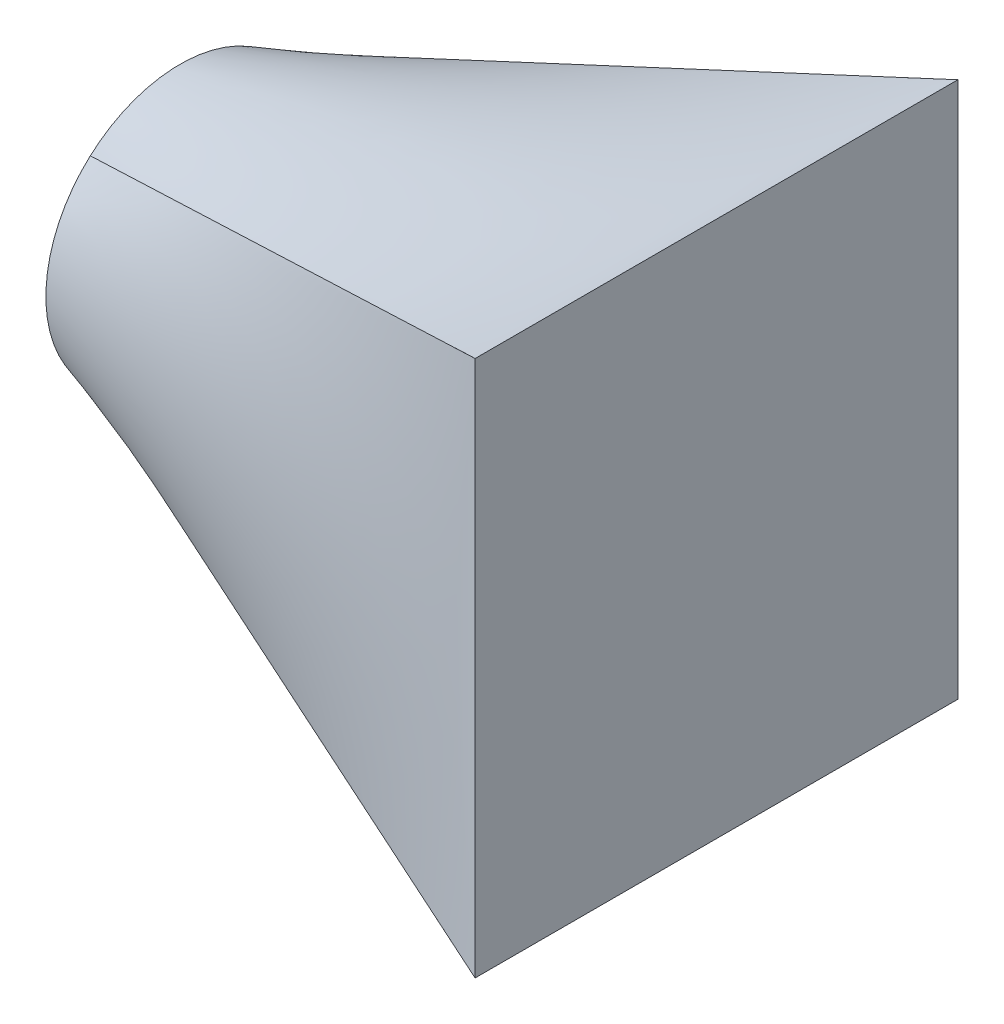
SolidWorks part; units mm, degrees
ref_plane "Přední rovina" through (0, 0, 0) normal (0, 0, 1) x (1, 0, 0)
ref_plane "Vrchní rovina" through (0, 0, 0) normal (0, 1, 0) x (1, 0, 0)
ref_plane "Pravá rovina" through (0, 0, 0) normal (1, 0, 0) x (0, 0, -1)
sketch "Skica1" plane through (0, 0, 0) normal (1, 0, 0) x (0, 0, -1)
  circle A0 centre (0, 0) radius 25
  dimension "D1" = 50
ref_plane "Rovina1" through (100, 0, 0) normal (1, 0, 0) x (0, 0, -1)
sketch "Skica2" plane through (100, 0, 0) normal (1, 0, 0) x (0, 0, -1)
  line L1 (-45, 50) -> (45, 50)
  line L2 (-45, 50) -> (-45, -50)
  line L3 (-45, -50) -> (45, -50)
  line L4 (45, 50) -> (45, -50)
  line L5 (-45, 50) -> (45, -50) construction
  line L6 (-45, -50) -> (45, 50) construction
  point P0 (0, 0)
  dimension "D1" = 90
  dimension "D2" = 100
loft "Spojit profily1" add profiles "Skica1", "Skica2"
